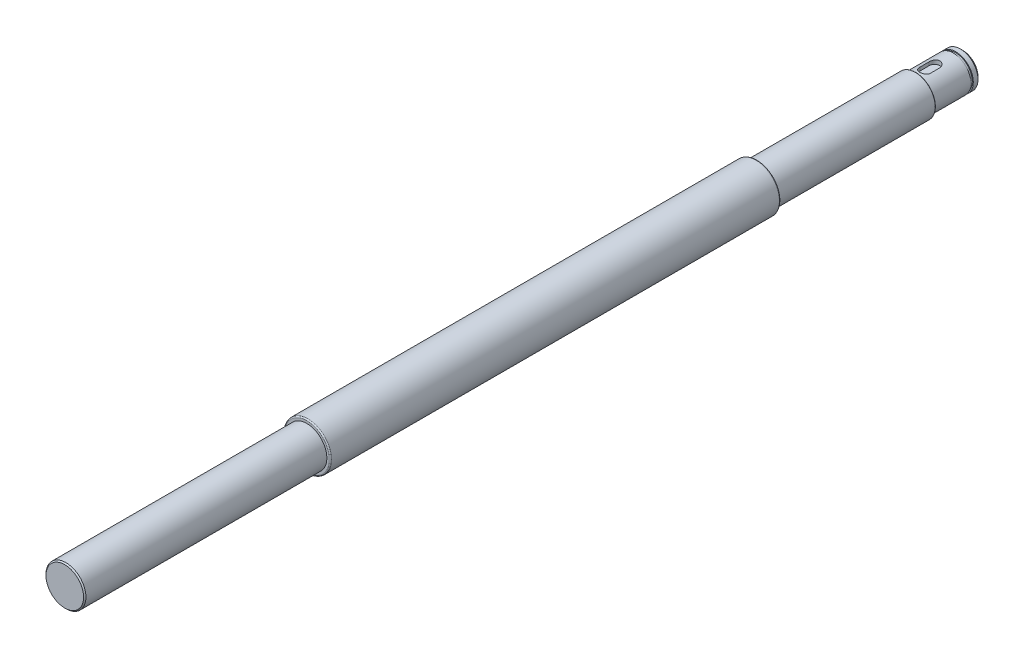
SolidWorks part; units mm, degrees
material "AISI 1045 Steel, cold drawn"
ref_plane "Front Plane" through (0, 0, 0) normal (0, 0, 1) x (1, 0, 0)
ref_plane "Top Plane" through (0, 0, 0) normal (0, 1, 0) x (1, 0, 0)
ref_plane "Right Plane" through (0, 0, 0) normal (1, 0, 0) x (0, 0, -1)
sketch "Sketch1" plane through (0, 0, 0) normal (0, 0, 1) x (1, 0, 0)
  circle A0 centre (0, 0) radius 10
  dimension "D1" = 20
extrude "Boss-Extrude1" add sketch "Sketch1" along normal blind 191.5
sketch "Sketch2" plane through (0, 0, 191.5) normal (0, 0, 1) x (1, 0, 0)
  circle A0 centre (0, 0) radius 8.5
  dimension "D1" = 17
extrude "Boss-Extrude2" add sketch "Sketch2" along normal blind 103
sketch "Sketch4" plane through (0, 0, 0) normal (0, 0, -1) x (-1, 0, 0)
  circle A0 centre (0, 0) radius 8.5
  dimension "D1" = 17
extrude "Boss-Extrude3" add sketch "Sketch4" along normal blind 67.5
fillet "Fillet1" radius 0.5 1 edges at (10, 0, 191.5)
fillet "Fillet2" radius 0.5 1 edges at (10, 0, 0)
ref_plane "Plane1" through (0, 7.5, 0) normal (0, 1, 0) x (-1, 0, 0)
sketch "Sketch6" plane through (0, 0, -67.5) normal (0, 0, -1) x (-1, 0, 0)
  circle A0 centre (0, 0) radius 7.5
  dimension "D1" = 15
extrude "Boss-Extrude4" add sketch "Sketch6" along normal blind 20
sketch "Sketch7" plane through (0, 7.5, 0) normal (0, 1, 0) x (-1, 0, 0)
  line L0 (0, -87.5) -> (0, -67.5) construction
  line L1 (-7.5, -87.5) -> (7.5, -87.5) construction
  line L2 (2.25, -75.5) -> (2.25, -71.5)
  line L4 (-2.25, -75.5) -> (-2.25, -71.5)
  arc A0 (2.25, -75.5) -> (-2.25, -75.5) centre (0, -75.5) cw
  arc A1 (2.25, -71.5) -> (-2.25, -71.5) centre (0, -71.5) ccw
  dimension "D4" = 12
  dimension "D1" = 4
  dimension "D2" = 4.5
  dimension "D3" = 2.25
extrude "Cut-Extrude1" cut sketch "Sketch7" against normal blind 1.8
ref_plane "Plane2" through (0, 0, -83.5) normal (0, 0, 1) x (1, 0, 0)
sketch "Sketch8" plane through (0, 0, -83.5) normal (0, 0, 1) x (1, 0, 0)
  circle A0 centre (0, 0) radius 7.075
  dimension "D1" = 14.15
extrude "Cut-Extrude-Thin1" cut sketch "Sketch8" against normal blind 1 thin
fillet "Fillet3" radius 0.25 1 edges at (-8.5, 0, -67.5)
chamfer "Chamfer1" distance 1 angle 45 1 edges at (-7.5, 0, -87.5)
chamfer "Chamfer2" distance 0.5 angle 45 1 edges at (8.5, 0, 294.5)
